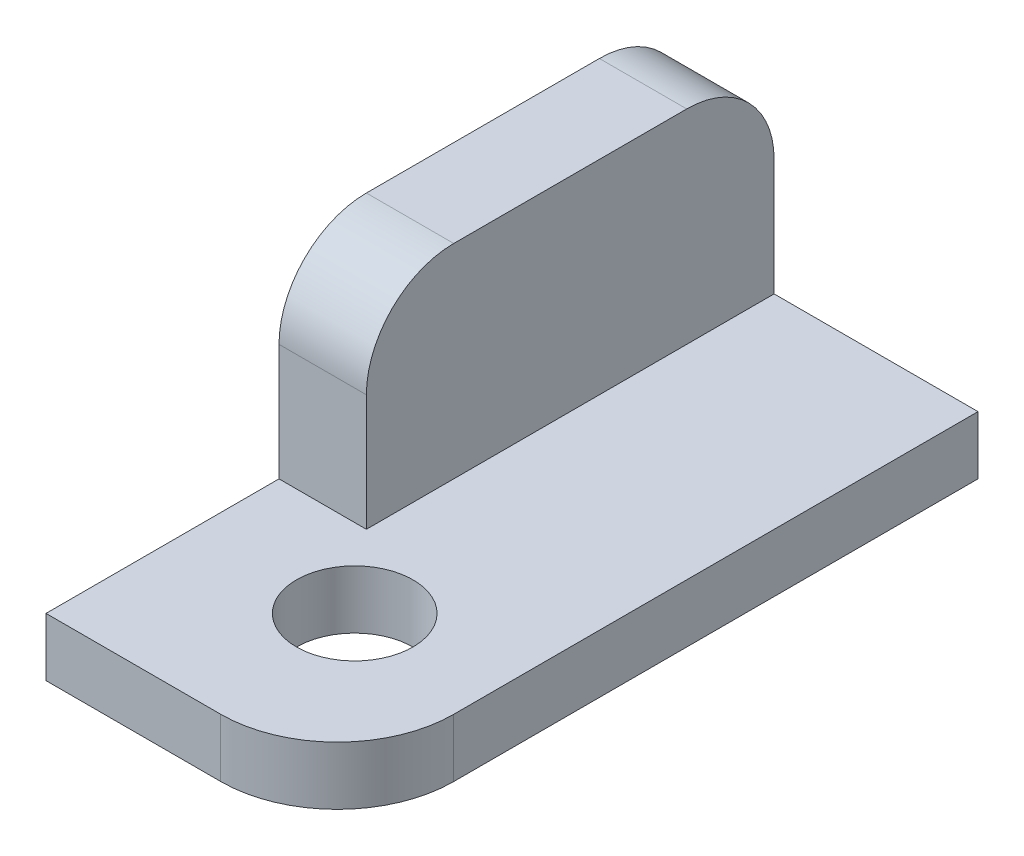
SolidWorks part; units mm, degrees
ref_plane "정면" through (0, 0, 0) normal (0, 0, 1) x (1, 0, 0)
ref_plane "윗면" through (0, 0, 0) normal (0, 1, 0) x (1, 0, 0)
ref_plane "우측면" through (0, 0, 0) normal (1, 0, 0) x (0, 0, -1)
sketch "스케치1" plane through (0, 0, 0) normal (1, 0, 0) x (0, 0, -1)
  line L0 (0, 0) -> (40, 0)
  line L1 (0, 0) -> (0, -10)
  line L2 (0, -10) -> (110, -10)
  line L3 (110, -10) -> (110, 35)
  line L4 (110, 35) -> (40, 35)
  line L5 (40, 35) -> (40, 0)
  dimension "D1" = 110
  dimension "D2" = 10
  dimension "D3" = 45
  dimension "D4" = 70
extrude "보스-돌출1" add sketch "스케치1" along normal blind 50
sketch "스케치2" plane through (0, 0, -40) normal (0, 0, 1) x (1, 0, 0)
  line L0 (50, 35) -> (0, 35) construction
  line L1 (50, 0) -> (15, 0)
  line L2 (50, 0) -> (50, 35)
  line L3 (50, 35) -> (15, 35)
  line L4 (15, 0) -> (15, 35)
  dimension "D1" = 15
extrude "컷-돌출1" cut sketch "스케치2" against normal blind 116
fillet "필렛1" radius 15 2 edges at (7.5, 35, -110) (7.5, 35, -40)
sketch "스케치3" plane through (0, 0, 0) normal (0, 1, 0) x (1, 0, 0)
  line L0 (26.5, 26.5) -> (0, 26.5) construction
  line L2 (0, 40) -> (0, 0) construction
  line L3 (50, 0) -> (0, 0) construction
  circle A0 centre (26.5, 26.5) radius 10
  dimension "D1" = 20
  dimension "D2" = 26.5
  dimension "D3" = 26.5
extrude "컷-돌출2" cut sketch "스케치3" against normal blind 10
fillet "필렛2" radius 20 1 edges at (50, -5, 0)
